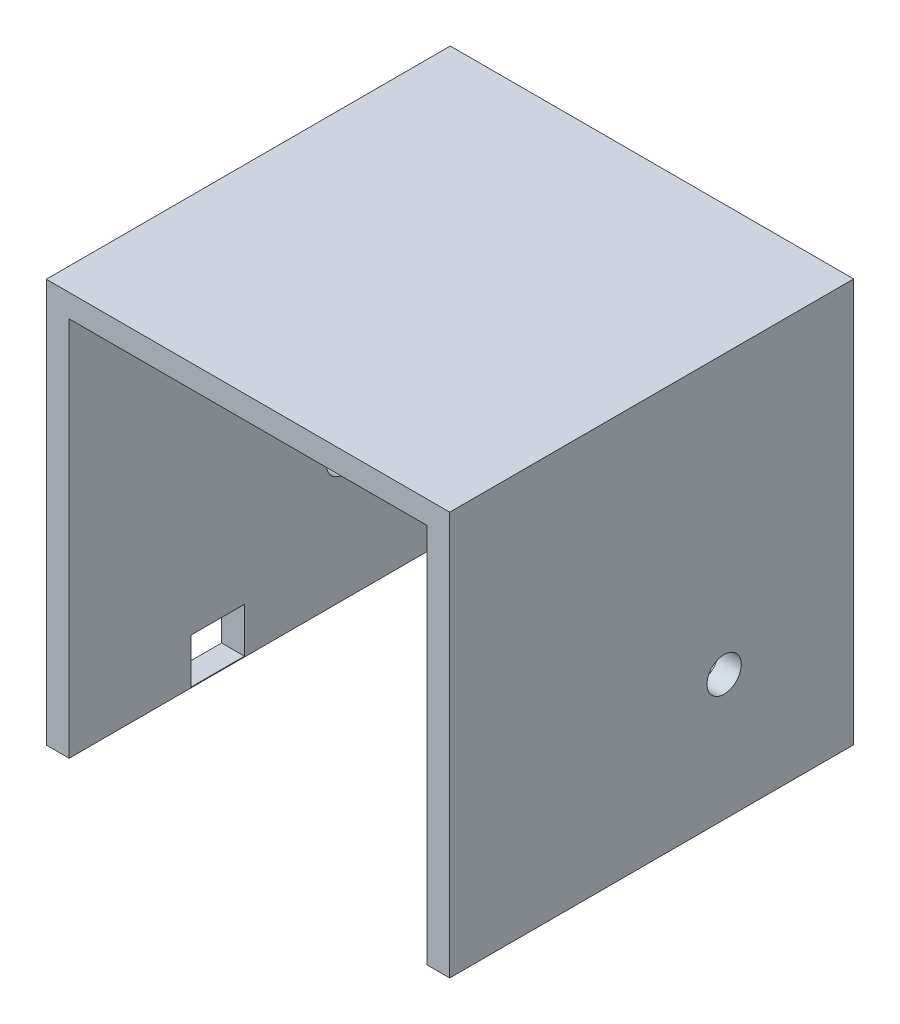
SolidWorks part; units mm, degrees
ref_plane "Front Plane" through (0, 0, 0) normal (0, 0, 1) x (1, 0, 0)
ref_plane "Top Plane" through (0, 0, 0) normal (0, 1, 0) x (1, 0, 0)
ref_plane "Right Plane" through (0, 0, 0) normal (1, 0, 0) x (0, 0, -1)
sketch "Sketch1" plane through (0, 0, 0) normal (0, 0, 1) x (1, 0, 0)
  line L0 (-248.8757, -247.3804) -> (-278.8757, -247.3804)
  line L4 (-248.8757, 251.9196) -> (-248.8757, -247.3804)
  line L5 (-248.8757, 251.9196) -> (220.4243, 251.9196)
  line L6 (220.4243, 251.9196) -> (220.4243, -247.3804)
  line L7 (250.4243, 281.9196) -> (-278.8757, 281.9196)
  line L10 (-278.8757, 281.9196) -> (-278.8757, -247.3804)
  line L11 (220.4243, -247.3804) -> (250.4243, -247.3804)
  line L12 (250.4243, -247.3804) -> (250.4243, 281.9196)
  point P0 (0, 0)
  point P6 (0, 0)
  dimension "D1" = 529.3
  dimension "D2" = 529.3
  dimension "D3" = 30
  dimension "D4" = 469.3
  dimension "D5" = 30
  dimension "D6" = 529.3
extrude "Boss-Extrude1" add sketch "Sketch1" along normal blind 530
sketch "Sketch2" plane through (250.4243, 0, 0) normal (1, 0, 0) x (0, 0, -1)
  line L0 (-530, -247.3804) -> (0, -247.3804) construction
  line L1 (-530, -247.3804) -> (-530, 281.9196) construction
  circle A0 centre (-170, -82.3804) radius 22.5
  dimension "D1" = 165
  dimension "D2" = 360
  dimension "D3" = 45
extrude "Cut-Extrude1" cut sketch "Sketch2" against normal through all both and the other way through all
sketch "Sketch3" plane through (-278.8757, 0, 0) normal (-1, 0, 0) x (0, 0, 1)
  line L2 (300, -187.3804) -> (370, -187.3804)
  line L5 (300, -187.3804) -> (300, -246.3804)
  line L6 (300, -246.3804) -> (370, -246.3804)
  line L7 (370, -246.3804) -> (370, -187.3804)
  line L8 (530, -247.3804) -> (0, -247.3804) construction
  line L9 (530, 281.9196) -> (530, -247.3804) construction
  dimension "D1" = 70
  dimension "D2" = 1
  dimension "D3" = 59
  dimension "D4" = 160
extrude "Cut-Extrude2" cut sketch "Sketch3" against normal blind 220
